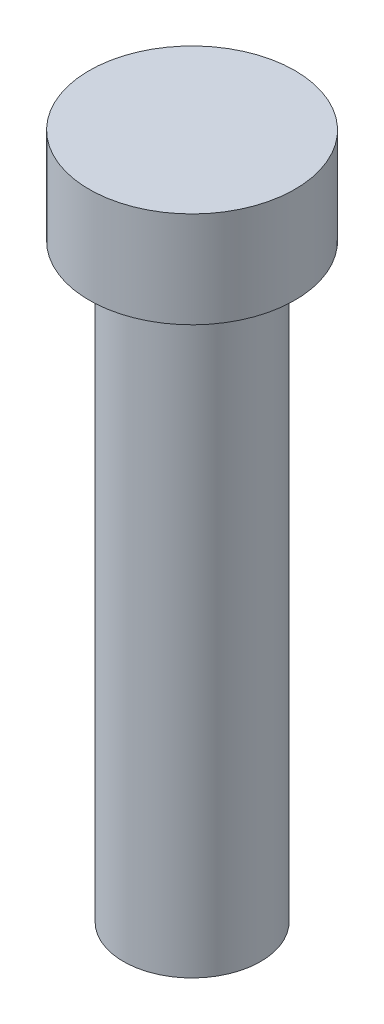
SolidWorks part; units mm, degrees
ref_plane "Front Plane" through (0, 0, 0) normal (0, 0, 1) x (1, 0, 0)
ref_plane "Top Plane" through (0, 0, 0) normal (0, 1, 0) x (1, 0, 0)
ref_plane "Right Plane" through (0, 0, 0) normal (1, 0, 0) x (0, 0, -1)
sketch "Sketch1" plane through (0, 0, 0) normal (0, 0, 1) x (1, 0, 0)
  line L0 (5, 0) -> (5, 43)
  line L1 (5, 43) -> (7.5, 43)
  line L2 (7.5, 43) -> (7.5, 50)
  line L3 (7.5, 50) -> (0, 50)
  line L4 (5, 0) -> (0, 0)
  line L5 (0, 0) -> (0, 50)
  point P2 (0.3464, 50)
  dimension "D1" = 5
  dimension "D2" = 7.5
  dimension "D3" = 7
  dimension "D4" = 50
revolve "Revolve1" add sketch "Sketch1" angle 360 about L5
